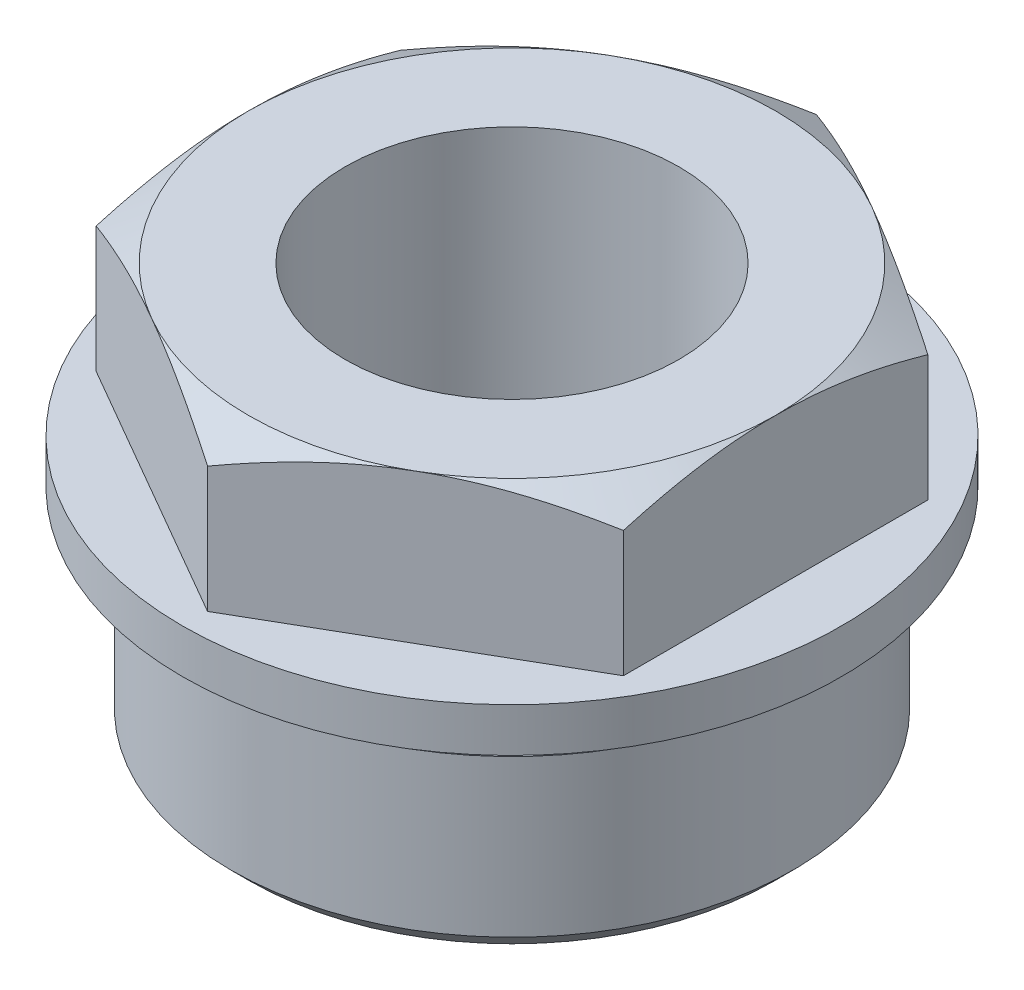
SolidWorks part; units mm, degrees
material "Бронза"
ref_plane "Спереди" through (0, 0, 0) normal (0, 0, 1) x (1, 0, 0)
ref_plane "Сверху" through (0, 0, 0) normal (0, 1, 0) x (1, 0, 0)
ref_plane "Справа" through (0, 0, 0) normal (1, 0, 0) x (0, 0, -1)
sketch "Эскиз1" plane through (0, 0, 0) normal (0, 0, 1) x (1, 0, 0)
  line L0 (0, 57.2608) -> (0, 0) construction
  line L1 (25, 0) -> (32, 0)
  line L2 (32, 0) -> (32, 20)
  line L3 (32, 20) -> (28, 20)
  line L4 (28, 20) -> (28, 24)
  line L5 (28, 24) -> (37.5, 24)
  line L6 (37.5, 24) -> (37.5, 29)
  line L7 (37.5, 29) -> (32.5, 29)
  line L8 (32.5, 29) -> (32.5, 42.5359)
  line L9 (32.5, 42.5359) -> (26.5, 46)
  line L10 (26.5, 46) -> (19, 46)
  line L11 (19, 46) -> (19, 5)
  line L12 (19, 5) -> (25, 5)
  line L13 (25, 5) -> (25, 0)
  dimension "D1" = 64
  dimension "D2" = 38
  dimension "D3" = 50
  dimension "D4" = 5
  dimension "D5" = 46
  dimension "D6" = 20
  dimension "D7" = 56
  dimension "D8" = 4
  dimension "D9" = 75
  dimension "D10" = 65
  dimension "D11" = 5
  dimension "D12" = 30
  dimension "D13" = 6
revolve "Повернуть1" add sketch "Эскиз1" angle 360 about L0
cosmetic thread "Условное изображение резьбы1" parameters "D2"=59.61
chamfer "Фаска1" distance 2.195 angle 45 1 edges at (0, 0, 32)
sketch "Эскиз2" plane through (0, 29, 0) normal (0, 1, 0) x (1, 0, 0)
  line L1 (0, 34.641) -> (-30, 17.3205)
  line L2 (-30, 17.3205) -> (-30, -17.3205)
  line L3 (-30, -17.3205) -> (0, -34.641)
  line L4 (0, -34.641) -> (30, -17.3205)
  line L5 (30, -17.3205) -> (30, 17.3205)
  line L6 (30, 17.3205) -> (0, 34.641)
  circle A0 centre (0, 0) radius 30 construction
  circle A2 centre (0, 0) radius 37.5
  circle A3 centre (0, 0) radius 37.5
  dimension "D1" = 60
  dimension "D2" = 0
extrude "Вырез-Вытянуть1" cut sketch "Эскиз2" along normal through all
sketch "Эскиз3" plane through (0, 29, 0) normal (0, 1, 0) x (1, 0, 0)
  line L0 (-4.1747, 32.2308) -> (-25.8253, 19.7308) construction
  line L1 (0, 34.641) -> (-30, 17.3205)
  line L2 (-30, 17.3205) -> (-30, -17.3205)
  line L3 (-30, -17.3205) -> (0, -34.641)
  line L4 (0, -34.641) -> (30, -17.3205)
  line L5 (30, -17.3205) -> (30, 17.3205)
  line L6 (30, 17.3205) -> (0, 34.641)
  circle A0 centre (0, 0) radius 30 construction
  circle A1 centre (0, 0) radius 25
  dimension "D1" = 50
extrude "Бобышка-Вытянуть1" add sketch "Эскиз3" along normal up to surface (17 mm away) up to face at (0, 46, 19)
sketch "Эскиз4" plane through (0, 0, 0) normal (0, 0, 1) x (1, 0, 0)
  line L0 (-30, 46) -> (-45, 46)
  line L1 (-45, 46) -> (-45, 37.3397)
  line L2 (-45, 37.3397) -> (-30, 46)
  line L3 (0, 0) -> (0, 54.1071) construction
  line L5 (-29.805, 0) -> (29.805, 0) construction
  dimension "D1" = 30
  dimension "D2" = 15
revolve "Вырез-Повернуть1" cut sketch "Эскиз4" angle 360 about L3
